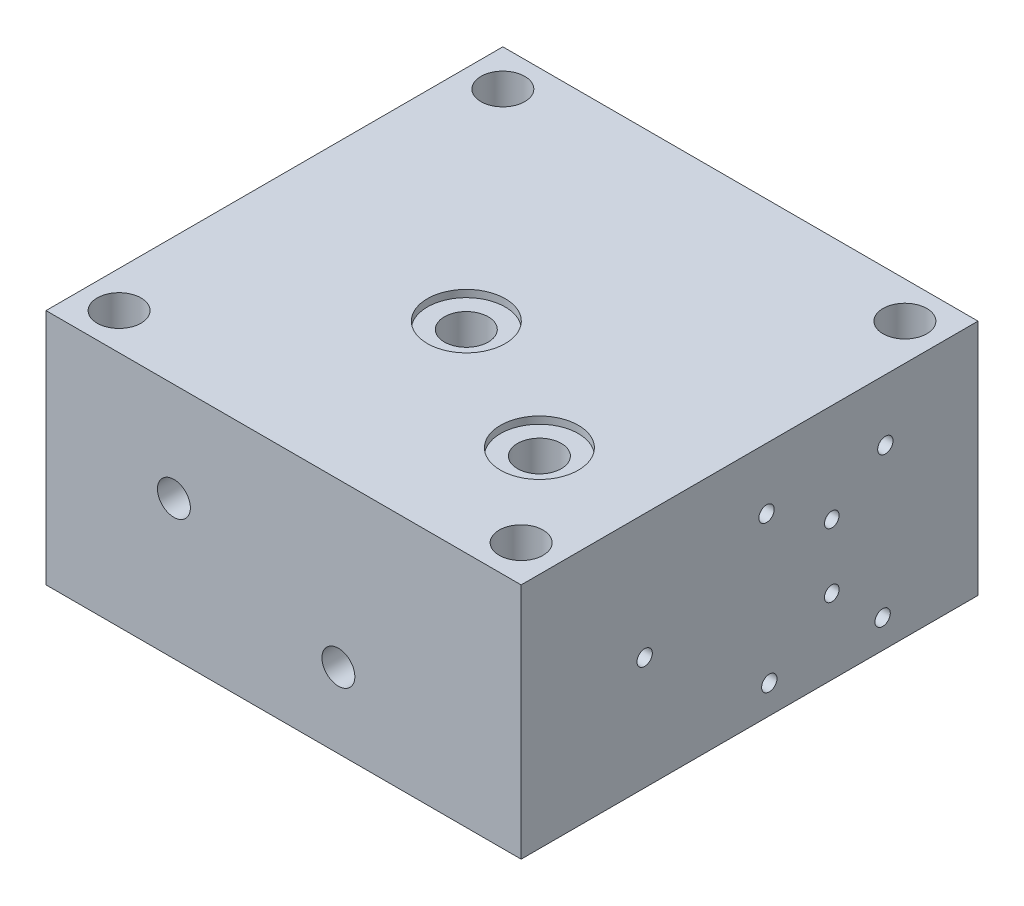
SolidWorks part; units mm, degrees
ref_plane "前视基准面" through (0, 0, 0) normal (0, 0, 1) x (1, 0, 0)
ref_plane "上视基准面" through (0, 0, 0) normal (0, 1, 0) x (1, 0, 0)
ref_plane "右视基准面" through (0, 0, 0) normal (1, 0, 0) x (0, 0, -1)
sketch "草图2" plane through (0, 0, 0) normal (0, 1, 0) x (1, 0, 0)
  line L1 (-65, -62.5) -> (65, -62.5)
  line L2 (-65, -62.5) -> (-65, 62.5)
  line L3 (-65, 62.5) -> (65, 62.5)
  line L4 (65, -62.5) -> (65, 62.5)
  line L5 (-65, -62.5) -> (65, 62.5) construction
  line L6 (-65, 62.5) -> (65, -62.5) construction
  circle A0 centre (-55, 52.5) radius 6
  circle A1 centre (55, 52.5) radius 6
  circle A2 centre (55, -52.5) radius 6
  circle A3 centre (-55, -52.5) radius 6
  point P0 (0, 0)
  dimension "D1" = 10
  dimension "D2" = 10
  dimension "D3" = 2
  dimension "D4" = 2
extrude "凸台-拉伸1" add sketch "草图2" along normal blind 65 contours A2 | A3 | A1 | L2 L3 L4 L1 | A0
sketch "草图19" plane through (-65, 0, 0) normal (-1, 0, 0) x (0, 0, 1)
  line L0 (-62.5, 65) -> (-62.5, 38)
  line L1 (-62.5, 65) -> (-62.5, 0) construction
  line L2 (-62.5, 38) -> (-22.5, 38)
hole_wizard "Ø4.0 (4) 直径孔5" positions "3D草图6" profile "草图20" hole size "Ø4.0" standard "GB" end condition through all
sketch3d "3D草图6"
  point P0 (-65, 38, -22.5)
sketch "草图20" plane through (-65, 38, -22.5) normal (0, 1, 0) x (0, 0, 1)
  line L0 (0, 0) -> (0, 130)
  line L1 (0, 130) -> (2, 130)
  line L2 (2, 130) -> (2, 0)
  line L5 (2, 0) -> (0, 0)
  line L11 (0, -6.35) -> (0, 107.95) construction
  dimension "通孔孔直径" = 4
  dimension "通孔孔深度" = 130
sketch "草图21" plane through (0, 0, -62.5) normal (0, 0, -1) x (-1, 0, 0)
  point P10 (-4.7, 9.8)
  point P11 (-12.2, 20.5)
  point P12 (-30.5, 9.8)
  point P13 (-23, 20.5)
  point P22 (-30.5, 31.2)
  point P23 (-4.7, 31.2)
  point P24 (-32.5, 20.5)
  point P25 (-17.6, 30.4)
  dimension "D3" = 27.8
  dimension "D4" = 12.9
  dimension "D5" = 10.7
  dimension "D6" = 20.6
  dimension "D7" = 21.4
  dimension "D8" = 25.8
  dimension "D1" = 7.5
  dimension "D2" = 18.3
sketch "草图26" plane through (65, 0, 0) normal (1, 0, 0) x (0, 0, -1)
  point P2 (-28.7046, 20.5)
  point P8 (5.4, 7.8)
  point P9 (4.65, 48.3)
  point P10 (37.15, 48.3)
  point P11 (36.4, 7.8)
  point P12 (22.4954, 38)
  point P13 (22.4954, 20.5)
  dimension "D1" = 40.5
  dimension "D2" = 0.75
  dimension "D3" = 31
  dimension "D4" = 31.75
  dimension "D5" = 30.2
  dimension "D6" = 12.7
hole_wizard "M5 螺纹孔3" positions "3D草图11" profile "草图27" tap size "M5" standard "GB"
sketch3d "3D草图11"
  point P0 (65, 48.3, -4.65)
  point P3 (65, 48.3, -37.15)
  point P6 (65, 7.8, -36.4)
  point P9 (65, 7.8, -5.4)
sketch "草图27" plane through (65, 48.3, -4.65) normal (0, 1, 0) x (0, 0, -1)
  line L0 (0, 0) -> (0, 13.2618)
  line L1 (0, 13.2618) -> (2.1, 12)
  line L2 (2.1, 12) -> (2.1, 0)
  line L5 (2.1, 0) -> (0, 0)
  line L10 (0, 13.2618) -> (-2.1, 12) construction
  line L11 (0, -6.35) -> (0, 107.95) construction
  dimension "螺纹孔钻头直径" = 4.2
  dimension "螺纹孔钻头深度" = 12
  dimension "导头角度" = 118
cosmetic thread "孔螺蚊线9" parameters "D1"=8, "D2"=5
cosmetic thread "孔螺蚊线10" parameters "D1"=8, "D2"=5
cosmetic thread "孔螺蚊线11" parameters "D1"=8, "D2"=5
cosmetic thread "孔螺蚊线12" parameters "D1"=8, "D2"=5
hole_wizard "Ø4.0 (4) 直径孔9" positions "3D草图12" profile "草图28" hole size "Ø4.0" standard "GB"
sketch3d "3D草图12"
  point P0 (65, 20.5, -22.4954)
sketch "草图28" plane through (65, 20.5, -22.4954) normal (0, 1, 0) x (0, 0, -1)
  line L0 (0, 0) -> (0, 33.7017)
  line L1 (0, 33.7017) -> (2, 32.5)
  line L2 (2, 32.5) -> (2, 0)
  line L5 (2, 0) -> (0, 0)
  line L10 (0, 33.7017) -> (-2, 32.5) construction
  line L11 (0, -6.35) -> (0, 107.95) construction
  dimension "孔直径" = 4
  dimension "孔深度" = 32.5
  dimension "导头角度" = 118
hole_wizard "Ø6.0 (6) 直径孔1" positions "3D草图13" profile "草图31" hole size "Ø6.0" standard "GB"
sketch3d "3D草图13"
  point P0 (32.5, 20.5, -62.5)
sketch "草图31" plane through (32.5, 20.5, -62.5) normal (1, 0, 0) x (0, 1, 0)
  line L0 (0, 0) -> (0, 43.8026)
  line L1 (0, 43.8026) -> (3, 42)
  line L2 (3, 42) -> (3, 0)
  line L5 (3, 0) -> (0, 0)
  line L10 (0, 43.8026) -> (-3, 42) construction
  line L11 (0, -6.35) -> (0, 107.95) construction
  dimension "孔直径" = 6
  dimension "孔深度" = 42
  dimension "导头角度" = 118
sketch "草图38" plane through (-65, 0, 0) normal (-1, 0, 0) x (0, 0, 1)
  point P0 (-22.5, 38)
  point P1 (-37, 52.5)
  point P6 (-8, 52.5)
  point P7 (-8, 23.5)
  point P8 (-37, 23.5)
  dimension "D1" = 14.5
  dimension "D2" = 14.5
  dimension "D3" = 2
  dimension "D4" = 2
hole_wizard "M6 螺纹孔1" positions "3D草图16" profile "草图39" tap size "M6" standard "GB"
sketch3d "3D草图16"
  point P0 (-65, 52.5, -37)
  point P3 (-65, 52.5, -8)
  point P6 (-65, 23.5, -37)
  point P9 (-65, 23.5, -8)
sketch "草图39" plane through (-65, 52.5, -37) normal (0, 1, 0) x (0, 0, 1)
  line L0 (0, 0) -> (0, 14.5022)
  line L1 (0, 14.5022) -> (2.5, 13)
  line L2 (2.5, 13) -> (2.5, 0)
  line L5 (2.5, 0) -> (0, 0)
  line L10 (0, 14.5022) -> (-2.5, 13) construction
  line L11 (0, -6.35) -> (0, 107.95) construction
  dimension "螺纹孔钻头直径" = 5
  dimension "螺纹孔钻头深度" = 13
  dimension "导头角度" = 118
cosmetic thread "孔螺蚊线13" parameters "D1"=8, "D2"=6
cosmetic thread "孔螺蚊线14" parameters "D1"=8, "D2"=6
cosmetic thread "孔螺蚊线15" parameters "D1"=8, "D2"=6
cosmetic thread "孔螺蚊线16" parameters "D1"=8, "D2"=6
sketch "草图40" plane through (0, 0, 62.5) normal (0, 0, 1) x (1, 0, 0)
  line L0 (-65, 38) -> (-30, 38)
hole_wizard "Ø4.0 (4) 直径孔11" positions "3D草图17" profile "草图41" hole size "Ø4.0" standard "GB"
sketch3d "3D草图17"
  point P0 (-30, 38, 62.5)
sketch "草图41" plane through (-30, 38, 62.5) normal (1, 0, 0) x (0, -1, 0)
  line L0 (0, 0) -> (0, 86.2017)
  line L1 (0, 86.2017) -> (2, 85)
  line L2 (2, 85) -> (2, 0)
  line L5 (2, 0) -> (0, 0)
  line L10 (0, 86.2017) -> (-2, 85) construction
  line L11 (0, -6.35) -> (0, 107.95) construction
  dimension "孔直径" = 4
  dimension "孔深度" = 85
  dimension "导头角度" = 118
hole_wizard "M10x1.0 螺纹孔1" positions "3D草图18" profile "草图42" tap size "M10x1.0" standard "GB"
sketch3d "3D草图18"
  point P0 (-30, 38, 62.5)
sketch "草图42" plane through (-30, 38, 62.5) normal (1, 0, 0) x (0, -1, 0)
  line L0 (0, 0) -> (0, 15.7039)
  line L1 (0, 15.7039) -> (4.5, 13)
  line L2 (4.5, 13) -> (4.5, 0)
  line L5 (4.5, 0) -> (0, 0)
  line L10 (0, 15.7039) -> (-4.5, 13) construction
  line L11 (0, -6.35) -> (0, 107.95) construction
  dimension "螺纹孔钻头直径" = 9
  dimension "螺纹孔钻头深度" = 13
  dimension "导头角度" = 118
cosmetic thread "孔螺蚊线17" parameters "D1"=8, "D2"=10
sketch "草图44" plane through (0, 0, 62.5) normal (0, 0, 1) x (1, 0, 0)
  line L0 (65, 0) -> (17.6, 0)
  line L1 (-65, 0) -> (65, 0) construction
  line L2 (17.6, 0) -> (17.6, 30.4)
sketch "草图46" plane through (0, 65, 0) normal (0, 1, 0) x (1, 0, 0)
  line L0 (65, -62.5) -> (35, -62.5)
  line L1 (65, -62.5) -> (17.6, -62.5) construction
  line L2 (35, -62.5) -> (35, -27.5)
  line L3 (65, 62.5) -> (-5, 62.5)
  line L4 (-65, 62.5) -> (65, 62.5) construction
  line L5 (-5, 62.5) -> (-5, -7.5)
hole_wizard "孔1" positions "3D草图22" profile "草图48" legacy
sketch3d "3D草图22"
  point P0 (-5, 65, 7.5)
  point P3 (35, 65, 27.5)
sketch "草图48" plane through (-5, 65, 7.5) normal (1, 0, 0) x (0, 0, 1)
  line L0 (0, 0) -> (0, 65)
  line L1 (0, 65) -> (6, 65)
  line L2 (6, 65) -> (6, 1.97)
  line L3 (6, 1.97) -> (10.65, 1.97)
  line L4 (10.65, 1.97) -> (10.65, 0)
  line L5 (10.65, 0) -> (0, 0)
  line L6 (0, 110) -> (0, -10) construction
  dimension "直径" = 12
  dimension "深度" = 65
  dimension "柱坑直径" = 21.3
  dimension "柱坑深度" = 1.97
sketch "草图50" plane through (0, 0, 0) normal (0, -1, 0) x (-1, 0, 0)
  line L0 (65, 62.5) -> (-23, 62.5)
  line L1 (65, 62.5) -> (-65, 62.5) construction
  line L2 (-23, 62.5) -> (-23, 3.7)
hole_wizard "Ø8.0 (8) 直径孔1" positions "3D草图24" profile "草图51" hole size "Ø8.0" standard "GB"
sketch3d "3D草图24"
  point P0 (23, 0, -3.7)
sketch "草图51" plane through (23, 0, -3.7) normal (1, 0, 0) x (0, 0, -1)
  line L0 (0, 0) -> (0, 17.9034)
  line L1 (0, 17.9034) -> (4, 15.5)
  line L2 (4, 15.5) -> (4, 0)
  line L5 (4, 0) -> (0, 0)
  line L10 (0, 17.9034) -> (-4, 15.5) construction
  line L11 (0, -6.35) -> (0, 107.95) construction
  dimension "孔直径" = 8
  dimension "孔深度" = 15.5
  dimension "导头角度" = 118
sketch "草图52" plane through (0, 0, -62.5) normal (0, 0, -1) x (-1, 0, 0)
  line L0 (-32.5, 20.5) -> (-23.7, 20.5)
  line L1 (-23.7, 20.5) -> (-23.7, 10.1)
  line L2 (-23.7, 20.5) -> (-23.7, 30.9)
  line L3 (-23.7, 20.5) -> (-15, 20.5)
  line L4 (-32.5, 20.5) -> (-32.5, 36)
  line L5 (-32.5, 36) -> (-45.2, 36)
  line L6 (-45.2, 36) -> (-4.7, 36)
  line L7 (-65, 36) -> (30, 36) construction
  line L8 (-4.7, 36) -> (-4.7, 5)
  line L9 (-45.2, 36) -> (-45.2, 5)
hole_wizard "M5 螺纹孔5" positions "3D草图25" profile "草图53" tap size "M5" standard "GB"
sketch3d "3D草图25"
  point P0 (4.7, 36, -62.5)
  point P3 (45.2, 36, -62.5)
  point P6 (45.2, 5, -62.5)
  point P9 (4.7, 5, -62.5)
sketch "草图53" plane through (4.7, 36, -62.5) normal (1, 0, 0) x (0, 1, 0)
  line L0 (0, 0) -> (0, 11.2618)
  line L1 (0, 11.2618) -> (2.1, 10)
  line L2 (2.1, 10) -> (2.1, 0)
  line L5 (2.1, 0) -> (0, 0)
  line L10 (0, 11.2618) -> (-2.1, 10) construction
  line L11 (0, -6.35) -> (0, 107.95) construction
  dimension "螺纹孔钻头直径" = 4.2
  dimension "螺纹孔钻头深度" = 10
  dimension "导头角度" = 118
cosmetic thread "孔螺蚊线25" parameters "D1"=8, "D2"=5
cosmetic thread "孔螺蚊线26" parameters "D1"=8, "D2"=5
cosmetic thread "孔螺蚊线27" parameters "D1"=8, "D2"=5
cosmetic thread "孔螺蚊线28" parameters "D1"=8, "D2"=5
hole_wizard "Ø6.0 (6) 直径孔2" positions "3D草图26" profile "草图54" hole size "Ø6.0" standard "GB"
sketch3d "3D草图26"
  point P0 (23.7, 10.1, -62.5)
sketch "草图54" plane through (23.7, 10.1, -62.5) normal (1, 0, 0) x (0, 1, 0)
  line L0 (0, 0) -> (0, 60.3026)
  line L1 (0, 60.3026) -> (3, 58.5)
  line L2 (3, 58.5) -> (3, 0)
  line L5 (3, 0) -> (0, 0)
  line L10 (0, 60.3026) -> (-3, 58.5) construction
  line L11 (0, -6.35) -> (0, 107.95) construction
  dimension "孔直径" = 6
  dimension "孔深度" = 58.5
  dimension "导头角度" = 118
hole_wizard "Ø6.0 (6) 直径孔3" positions "3D草图27" profile "草图55" hole size "Ø6.0" standard "GB"
sketch3d "3D草图27"
  point P0 (23.7, 30.9, -62.5)
sketch "草图55" plane through (23.7, 30.9, -62.5) normal (1, 0, 0) x (0, 1, 0)
  line L0 (0, 0) -> (0, 91.8026)
  line L1 (0, 91.8026) -> (3, 90)
  line L2 (3, 90) -> (3, 0)
  line L5 (3, 0) -> (0, 0)
  line L10 (0, 91.8026) -> (-3, 90) construction
  line L11 (0, -6.35) -> (0, 107.95) construction
  dimension "孔直径" = 6
  dimension "孔深度" = 90
  dimension "导头角度" = 118
sketch "草图56" plane through (65, 0, 0) normal (1, 0, 0) x (0, 0, -1)
  line L1 (62.5, 0) -> (-28.7046, 0)
  line L2 (-62.5, 0) -> (62.5, 0) construction
  line L3 (-28.7046, 0) -> (-28.7046, 30.9)
hole_wizard "M5 螺纹孔8" positions "3D草图30" profile "草图61" tap size "M5" standard "GB"
sketch3d "3D草图30"
  point P0 (65, 30.9, 28.7046)
sketch "草图61" plane through (65, 30.9, 28.7046) normal (0, 1, 0) x (0, 0, -1)
  line L0 (0, 0) -> (0, 42.5718)
  line L1 (0, 42.5718) -> (2.1, 41.31)
  line L2 (2.1, 41.31) -> (2.1, 0)
  line L5 (2.1, 0) -> (0, 0)
  line L10 (0, 42.5718) -> (-2.1, 41.31) construction
  line L11 (0, -6.35) -> (0, 107.95) construction
  dimension "螺纹孔钻头直径" = 4.2
  dimension "螺纹孔钻头深度" = 41.31
  dimension "导头角度" = 118
cosmetic thread "孔螺蚊线31" parameters "D1"=10, "D2"=5
hole_wizard "Ø6.0 (6) 直径孔4" positions "3D草图31" profile "草图62" hole size "Ø6.0" standard "GB" end condition through all
sketch3d "3D草图31"
  point P0 (15, 20.5, -62.5)
sketch "草图62" plane through (15, 20.5, -62.5) normal (1, 0, 0) x (0, 1, 0)
  line L0 (0, 0) -> (0, 125)
  line L1 (0, 125) -> (3, 125)
  line L2 (3, 125) -> (3, 0)
  line L5 (3, 0) -> (0, 0)
  line L11 (0, -6.35) -> (0, 107.95) construction
  dimension "通孔孔直径" = 6
  dimension "通孔孔深度" = 125
sketch "草图65" plane through (0, 0, 62.5) normal (0, 0, 1) x (1, 0, 0)
  line L0 (65, 0) -> (15, 0)
  line L1 (-65, 0) -> (65, 0) construction
  line L2 (15, 0) -> (15, 20.5)
hole_wizard "M10x1.0 螺纹孔2" positions "3D草图32" profile "草图66" tap size "M10x1.0" standard "GB"
sketch3d "3D草图32"
  point P0 (15, 20.5, 62.5)
sketch "草图66" plane through (15, 20.5, 62.5) normal (1, 0, 0) x (0, -1, 0)
  line L0 (0, 0) -> (0, 15.7039)
  line L1 (0, 15.7039) -> (4.5, 13)
  line L2 (4.5, 13) -> (4.5, 0)
  line L5 (4.5, 0) -> (0, 0)
  line L10 (0, 15.7039) -> (-4.5, 13) construction
  line L11 (0, -6.35) -> (0, 107.95) construction
  dimension "螺纹孔钻头直径" = 9
  dimension "螺纹孔钻头深度" = 13
  dimension "导头角度" = 118
cosmetic thread "孔螺蚊线32" parameters "D1"=8, "D2"=10
